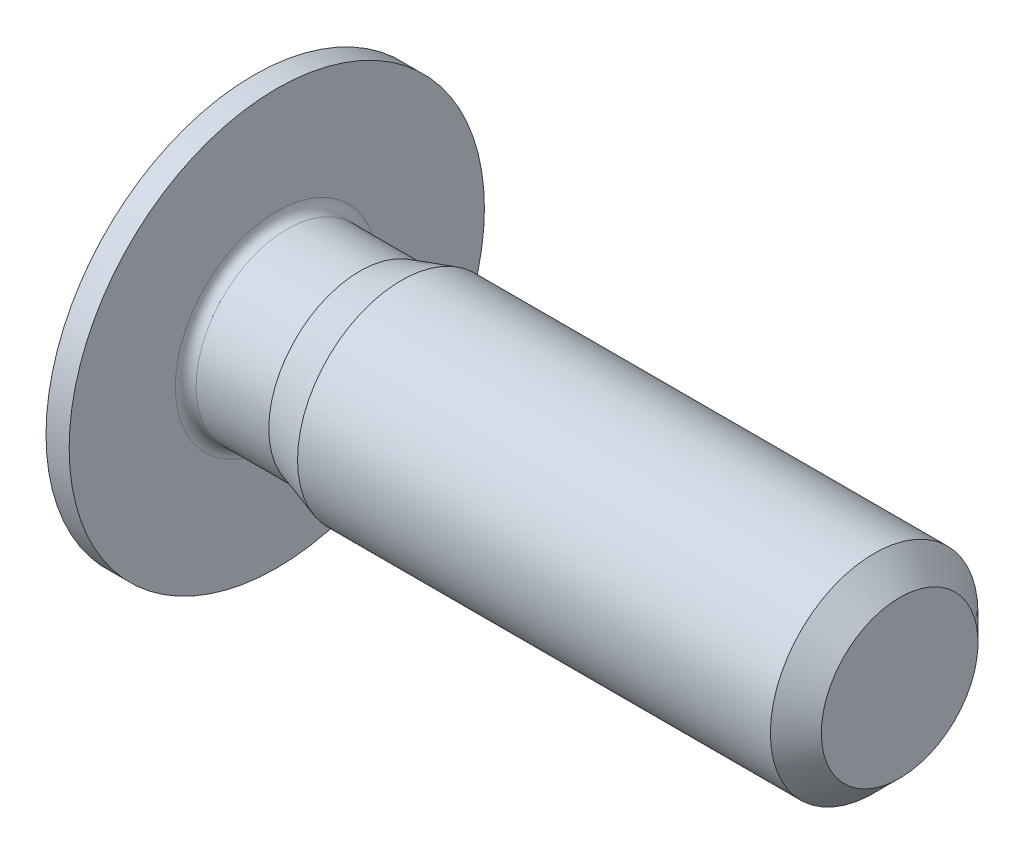
SolidWorks part; units mm, degrees
material "AISI 304"
ref_plane "正面" through (0, 0, 0) normal (0, 0, 1) x (1, 0, 0)
ref_plane "平面" through (0, 0, 0) normal (0, 1, 0) x (1, 0, 0)
ref_plane "右側面" through (0, 0, 0) normal (1, 0, 0) x (0, 0, -1)
ref_plane "Plane1" through (0, 0, 0) normal (0, 0, 1) x (1, 0, 0)
sketch "Sketch1" plane through (0, 0, 0) normal (0, 0, 1) x (1, 0, 0)
  line L0 (-0.5, 0) -> (-0.5, 1.52)
  line L1 (-0.5, 1.52) -> (-0.2229, 2)
  line L2 (-0.2229, 2) -> (0, 2)
  line L3 (0, 2) -> (0, 0.9773)
  line L4 (0.1, 0.8772) -> (0.8, 0.8772)
  line L5 (0.8, 0.8772) -> (1.2, 1)
  line L6 (1.2, 1) -> (5.7545, 1)
  line L7 (5.7545, 1) -> (6, 0.7545)
  line L8 (6, 0.7545) -> (6, 0)
  line L9 (6, 0) -> (-0.5, 0)
  line L10 (6, 0) -> (-0.5, 0) construction
  arc A0 (0, 0.9773) -> (0.1, 0.8772) centre (0.1, 0.9772) ccw
revolve "Revolve1" add sketch "Sketch1" angle 360 about L10
cosmetic thread "Cosmetic Thread1" parameters "D1"=4.8, "D2"=1.509
ref_plane "Plane2" through (0, 0, 0) normal (0, 0, 1) x (1, 0, 0)
sketch "Sketch2" plane through (0, 0, 0) normal (0, 0, 1) x (1, 0, 0)
  line L0 (-0.5, 0) -> (-0.5, 0.65)
  line L1 (-0.5, 0.65) -> (0.7, 0.65)
  line L2 (0.7, 0.65) -> (1.0753, 0)
  line L3 (1.0753, 0) -> (-0.5, 0)
  line L4 (1.0753, 0) -> (-0.5, 0) construction
revolve "Cut-Revolve1" cut sketch "Sketch2" angle 360 about L4
ref_plane "Plane3" through (-0.5, 0, 0) normal (1, 0, 0) x (0, 0, -1)
sketch "Sketch3" plane through (-0.5, 0, 0) normal (1, 0, 0) x (0, 0, -1)
  line L0 (-0.65, -0.3753) -> (0, -0.7506)
  line L1 (0, -0.7506) -> (0.65, -0.3753)
  line L2 (0.65, -0.3753) -> (0.65, 0.3753)
  line L3 (0.65, 0.3753) -> (0, 0.7506)
  line L4 (0, 0.7506) -> (-0.65, 0.3753)
  line L5 (-0.65, 0.3753) -> (-0.65, -0.3753)
extrude "Cut-Extrude1" cut sketch "Sketch3" along normal blind 1.2
